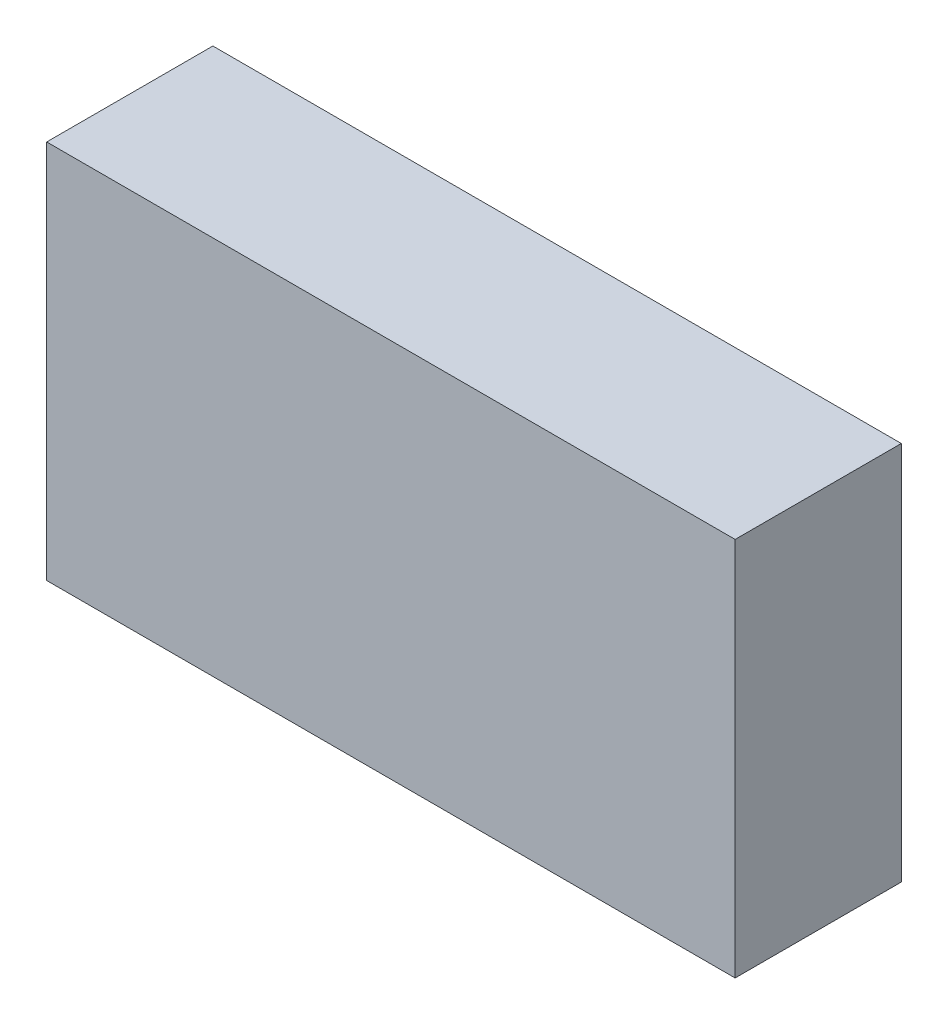
SolidWorks part; units mm, degrees
ref_plane "Front Plane" through (0, 0, 0) normal (0, 0, 1) x (1, 0, 0)
ref_plane "Top Plane" through (0, 0, 0) normal (0, 1, 0) x (1, 0, 0)
ref_plane "Right Plane" through (0, 0, 0) normal (1, 0, 0) x (0, 0, -1)
sketch "Sketch1" plane through (0, 0, 0) normal (0, 0, 1) x (1, 0, 0)
  line L1 (-29, 16) -> (29, 16)
  line L2 (-29, 16) -> (-29, -16)
  line L3 (-29, -16) -> (29, -16)
  line L4 (29, 16) -> (29, -16)
  line L5 (-29, 16) -> (29, -16) construction
  line L6 (-29, -16) -> (29, 16) construction
  point P0 (0, 0)
  dimension "D1" = 58
  dimension "D2" = 32
extrude "Boss-Extrude1" add sketch "Sketch1" along normal blind 14
